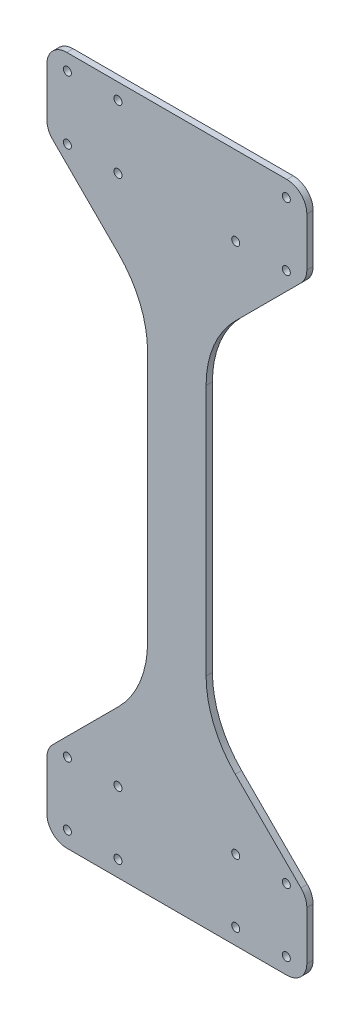
SolidWorks part; units mm, degrees
ref_plane "Front Plane" through (0, 0, 0) normal (0, 0, 1) x (1, 0, 0)
ref_plane "Top Plane" through (0, 0, 0) normal (0, 1, 0) x (1, 0, 0)
ref_plane "Right Plane" through (0, 0, 0) normal (1, 0, 0) x (0, 0, -1)
sketch "Sketch1" plane through (0, 0, 0) normal (0, 0, 1) x (1, 0, 0)
  line L0 (39.3854, -40.0501) -> (39.3854, -52.4111) construction
  line L1 (165.9345, -56.675) -> (165.9345, -42.05) construction
  line L2 (157.3152, -8.05) -> (165.9345, -16.6693)
  line L3 (157.3152, 245.3495) -> (165.9345, 253.9688)
  line L4 (39.3854, -40.0501) -> (39.3854, -52.4111)
  line L5 (165.9345, -56.675) -> (165.9345, -42.05)
  line L6 (165.9345, 245.3495) -> (39.3854, 245.3495)
  line L7 (165.9345, 279.3495) -> (165.9345, 245.3495)
  line L8 (39.3854, -52.4111) -> (165.9345, -56.675)
  line L9 (39.3854, 289.7105) -> (165.9345, 293.9745)
  line L10 (39.3854, -40.0501) -> (39.3854, -16.6693)
  line L11 (165.9345, -42.05) -> (165.9345, -16.6693)
  line L12 (157.3152, -8.05) -> (48.0047, -8.0501)
  line L13 (42.1433, 0) -> (42.1433, 237.2995) construction
  line L14 (42.1433, 118.6497) -> (215.0534, 118.6497) construction
  line L15 (165.9345, 293.9745) -> (165.9345, 279.3495)
  line L16 (39.3854, 277.3495) -> (39.3854, 245.3495)
  line L17 (39.3854, 277.3495) -> (39.3854, 289.7105)
  line L18 (102.66, -54.5431) -> (102.66, 291.8425) construction
  line L19 (102.66, 291.8425) -> (73.0854, -499321.8282) construction
  line L20 (39.3854, -16.6693) -> (89.96, 33.9052)
  line L21 (89.96, -8.05) -> (115.36, -8.05)
  line L22 (89.96, -8.05) -> (89.96, 245.3495)
  line L23 (89.96, 245.3495) -> (115.36, 245.3495)
  line L24 (115.36, -8.05) -> (115.36, 245.3495)
  line L25 (89.96, -8.05) -> (115.36, 245.3495) construction
  line L26 (89.96, 245.3495) -> (115.36, -8.05) construction
  line L27 (115.36, 33.9052) -> (157.3152, -8.05)
  line L28 (115.36, 203.3943) -> (157.3152, 245.3495)
  line L29 (39.3854, 253.9688) -> (89.96, 203.3943)
  arc A0 (157.6345, 249.9303) -> (157.6345, 253.9689) centre (157.6345, 251.9496) cw
  arc A1 (157.6345, 253.9689) -> (157.6345, 249.9303) centre (157.6345, 251.9496) cw
  arc A2 (73.0854, 249.9303) -> (73.0854, 253.9689) centre (73.0854, 251.9496) ccw
  arc A3 (73.0854, 253.9689) -> (73.0854, 249.9303) centre (73.0854, 251.9496) ccw
  arc A4 (73.0854, 249.9303) -> (73.0854, 253.9689) centre (73.0854, 251.9496) ccw
  arc A5 (73.0854, 253.9689) -> (73.0854, 249.9303) centre (73.0854, 251.9496) ccw
  arc A6 (47.6854, 249.9303) -> (47.6854, 253.9689) centre (47.6854, 251.9496) cw
  arc A7 (47.6854, 253.9689) -> (47.6854, 249.9303) centre (47.6854, 251.9496) cw
  arc A10 (47.6854, 281.6802) -> (47.6854, 285.7188) centre (47.6854, 283.6995) cw
  arc A11 (47.6854, 285.7188) -> (47.6854, 281.6802) centre (47.6854, 283.6995) cw
  arc A14 (157.6345, -48.4194) -> (157.6345, -44.3807) centre (157.6345, -46.4001) ccw
  arc A15 (157.6345, -44.3807) -> (157.6345, -48.4194) centre (157.6345, -46.4001) ccw
  arc A16 (157.6345, -48.4194) -> (157.6345, -44.3807) centre (157.6345, -46.4001) ccw
  arc A17 (157.6345, -44.3807) -> (157.6345, -48.4194) centre (157.6345, -46.4001) ccw
  arc A18 (73.0854, 281.6802) -> (73.0854, 285.7188) centre (73.0854, 283.6995) cw
  arc A19 (73.0854, 285.7188) -> (73.0854, 281.6802) centre (73.0854, 283.6995) cw
  arc A22 (157.6345, -16.6693) -> (157.6345, -12.6307) centre (157.6345, -14.65) ccw
  arc A23 (157.6345, -12.6307) -> (157.6345, -16.6693) centre (157.6345, -14.65) ccw
  arc A24 (157.6345, -16.6693) -> (157.6345, -12.6307) centre (157.6345, -14.65) ccw
  arc A25 (157.6345, -12.6307) -> (157.6345, -16.6693) centre (157.6345, -14.65) ccw
  arc A26 (73.0854, -16.6693) -> (73.0854, -12.6307) centre (73.0854, -14.65) ccw
  arc A27 (73.0854, -12.6307) -> (73.0854, -16.6693) centre (73.0854, -14.65) ccw
  arc A28 (73.0854, -16.6693) -> (73.0854, -12.6307) centre (73.0854, -14.65) ccw
  arc A29 (73.0854, -12.6307) -> (73.0854, -16.6693) centre (73.0854, -14.65) ccw
  arc A30 (73.0854, 249.9303) -> (73.0854, 253.9689) centre (73.0854, 251.9496) cw
  arc A31 (73.0854, 253.9689) -> (73.0854, 249.9303) centre (73.0854, 251.9496) cw
  arc A34 (157.6345, 249.9303) -> (157.6345, 253.9689) centre (157.6345, 251.9496) ccw
  arc A35 (157.6345, 253.9689) -> (157.6345, 249.9303) centre (157.6345, 251.9496) ccw
  arc A36 (157.6345, 249.9303) -> (157.6345, 253.9689) centre (157.6345, 251.9496) ccw
  arc A37 (157.6345, 253.9689) -> (157.6345, 249.9303) centre (157.6345, 251.9496) ccw
  arc A38 (47.6854, 249.9303) -> (47.6854, 253.9689) centre (47.6854, 251.9496) ccw
  arc A39 (47.6854, 253.9689) -> (47.6854, 249.9303) centre (47.6854, 251.9496) ccw
  arc A40 (47.6854, 249.9303) -> (47.6854, 253.9689) centre (47.6854, 251.9496) ccw
  arc A41 (47.6854, 253.9689) -> (47.6854, 249.9303) centre (47.6854, 251.9496) ccw
  arc A42 (73.0854, -48.4194) -> (73.0854, -44.3807) centre (73.0854, -46.4001) ccw
  arc A43 (73.0854, -44.3807) -> (73.0854, -48.4194) centre (73.0854, -46.4001) ccw
  arc A44 (73.0854, -48.4194) -> (73.0854, -44.3807) centre (73.0854, -46.4001) ccw
  arc A45 (73.0854, -44.3807) -> (73.0854, -48.4194) centre (73.0854, -46.4001) ccw
  arc A46 (132.2345, 249.9303) -> (132.2345, 253.9689) centre (132.2345, 251.9496) ccw
  arc A47 (132.2345, 253.9689) -> (132.2345, 249.9303) centre (132.2345, 251.9496) ccw
  arc A48 (132.2345, 249.9303) -> (132.2345, 253.9689) centre (132.2345, 251.9496) ccw
  arc A49 (132.2345, 253.9689) -> (132.2345, 249.9303) centre (132.2345, 251.9496) ccw
  arc A50 (47.6854, -48.4194) -> (47.6854, -44.3808) centre (47.6854, -46.4001) ccw
  arc A51 (47.6854, -44.3808) -> (47.6854, -48.4194) centre (47.6854, -46.4001) ccw
  arc A52 (47.6854, -48.4194) -> (47.6854, -44.3808) centre (47.6854, -46.4001) ccw
  arc A53 (47.6854, -44.3808) -> (47.6854, -48.4194) centre (47.6854, -46.4001) ccw
  arc A54 (47.6854, -16.6693) -> (47.6854, -12.6307) centre (47.6854, -14.65) ccw
  arc A55 (47.6854, -12.6307) -> (47.6854, -16.6693) centre (47.6854, -14.65) ccw
  arc A56 (47.6854, -16.6693) -> (47.6854, -12.6307) centre (47.6854, -14.65) ccw
  arc A57 (47.6854, -12.6307) -> (47.6854, -16.6693) centre (47.6854, -14.65) ccw
  arc A58 (157.6345, 281.6802) -> (157.6345, 285.7188) centre (157.6345, 283.6995) cw
  arc A59 (157.6345, 285.7188) -> (157.6345, 281.6802) centre (157.6345, 283.6995) cw
  arc A62 (132.2345, -16.6693) -> (132.2345, -12.6307) centre (132.2345, -14.65) ccw
  arc A63 (132.2345, -12.6307) -> (132.2345, -16.6693) centre (132.2345, -14.65) ccw
  arc A64 (132.2345, -16.6693) -> (132.2345, -12.6307) centre (132.2345, -14.65) ccw
  arc A65 (132.2345, -12.6307) -> (132.2345, -16.6693) centre (132.2345, -14.65) ccw
  arc A66 (132.2345, -48.4194) -> (132.2345, -44.3808) centre (132.2345, -46.4001) ccw
  arc A67 (132.2345, -44.3808) -> (132.2345, -48.4194) centre (132.2345, -46.4001) ccw
  arc A68 (132.2345, -48.4194) -> (132.2345, -44.3808) centre (132.2345, -46.4001) ccw
  arc A69 (132.2345, -44.3808) -> (132.2345, -48.4194) centre (132.2345, -46.4001) ccw
  point P62 (102.66, 118.6497)
  dimension "D3" = 0
  dimension "D2" = 25.4
  dimension "D1" = 0
  dimension "D4" = 0
  dimension "D5" = 0
  dimension "D6" = 0
  dimension "D7" = 0
  dimension "D9" = 0
  dimension "D10" = 0
  dimension "D11" = 0
  dimension "D12" = 0
  dimension "D13" = 0
  dimension "D14" = 0
extrude "Boss-Extrude1" add sketch "Sketch1" along normal blind 3.175 contours L20 L10 L4 L8 L5 L11 L2 L12 A69 A68 A65 A64 A57 A56 A53 A52 A45 A44 A29 A28 A25 A24 A17 A16 | L27 L24 L12 | L12 L24 L6 L22 | L12 L22 L20 | L16 L29 L6 L3 L7 L15 L9 L17 A49 A48 A5 A4 A0 A1 A6 A7 A10 A11 A18 A19 A58 A59 | L24 L28 L6 | L6 L29 L22
sketch "Sketch2" plane through (0, 0, 3.175) normal (0, 0, 1) x (1, 0, 0)
  line L0 (165.9345, -56.675) -> (165.9345, -16.6693) construction
  line L1 (39.3854, -52.4111) -> (84.3854, -52.4111)
  line L2 (39.3854, -52.4111) -> (39.3854, -7.4111)
  line L3 (39.3854, -7.4111) -> (84.3854, -7.4111)
  line L4 (84.3854, -52.4111) -> (84.3854, -7.4111)
  line L5 (165.9345, -52.4111) -> (120.9345, -52.4111)
  line L6 (165.9345, -52.4111) -> (165.9345, -7.4111)
  line L7 (165.9345, -7.4111) -> (120.9345, -7.4111)
  line L8 (120.9345, -52.4111) -> (120.9345, -7.4111)
  line L9 (89.96, 118.6497) -> (115.36, 118.6497) construction
  line L10 (89.96, 33.9052) -> (89.96, 203.3943) construction
  line L11 (115.36, 33.9052) -> (115.36, 203.3943) construction
  line L12 (165.9345, 289.7105) -> (120.9345, 289.7105)
  line L13 (39.3854, 289.7105) -> (84.3854, 289.7105)
  line L14 (84.3854, -52.4111) -> (120.9345, -52.4111)
  line L15 (84.3854, 289.7105) -> (120.9345, 289.7105)
  line M9 (39.3854, -52.4111) -> (165.9345, -56.675)
  line M10 (165.9345, -56.675) -> (165.9345, -16.6693)
  line M14 (165.9345, 253.9688) -> (165.9345, 293.9745)
  line M15 (165.9345, 293.9745) -> (39.3854, 289.7105)
  dimension "D1" = 45
extrude "Cut-Extrude1" cut sketch "Sketch2" against normal blind 10 contours L14 L1 L5 M9 M10 | L13 L15 L12 M14 M15
sketch "Sketch3" plane through (0, 0, 3.175) normal (0, 0, 1) x (1, 0, 0)
  line L25 (37.3854, -15.8409) -> (37.3854, -54.4111)
  line L26 (37.3854, -54.4111) -> (167.9345, -54.4111)
  line L27 (167.9345, -54.4111) -> (167.9345, -15.8409)
  line L28 (167.9345, -15.8409) -> (117.36, 34.7337)
  line L29 (117.36, 34.7337) -> (117.36, 202.5658)
  line L30 (117.36, 202.5658) -> (167.9345, 253.1404)
  line L31 (167.9345, 253.1404) -> (167.9345, 291.7105)
  line L32 (167.9345, 291.7105) -> (37.3854, 291.7105)
  line L33 (37.3854, 291.7105) -> (37.3854, 253.1404)
  line L34 (37.3854, 253.1404) -> (87.96, 202.5658)
  line L35 (87.96, 202.5658) -> (87.96, 34.7337)
  line L36 (87.96, 34.7337) -> (37.3854, -15.8409)
  line L37 (37.3854, -15.8409) -> (37.3854, -54.4111)
  line L38 (37.3854, -54.4111) -> (167.9345, -54.4111)
  line L39 (167.9345, -54.4111) -> (167.9345, -15.8409)
  line L40 (167.9345, -15.8409) -> (117.36, 34.7337)
  line L41 (117.36, 34.7337) -> (117.36, 202.5658)
  line L42 (117.36, 202.5658) -> (167.9345, 253.1404)
  line L43 (167.9345, 253.1404) -> (167.9345, 291.7105)
  line L44 (167.9345, 291.7105) -> (37.3854, 291.7105)
  line L45 (37.3854, 291.7105) -> (37.3854, 253.1404)
  line L46 (37.3854, 253.1404) -> (87.96, 202.5658)
  line L47 (87.96, 202.5658) -> (87.96, 34.7337)
  line L48 (87.96, 34.7337) -> (37.3854, -15.8409)
  circle A1 centre (132.2345, -46.4001) radius 2.0193
  circle A2 centre (132.2345, -46.4001) radius 2.0193
  circle A3 centre (132.2345, -14.65) radius 2.0193
  circle A4 centre (132.2345, -14.65) radius 2.0193
  circle A5 centre (47.6854, -14.65) radius 2.0193
  circle A6 centre (47.6854, -14.65) radius 2.0193
  circle A7 centre (47.6854, -46.4001) radius 2.0193
  circle A8 centre (47.6854, -46.4001) radius 2.0193
  circle A9 centre (73.0854, -46.4001) radius 2.0193
  circle A10 centre (73.0854, -46.4001) radius 2.0193
  circle A11 centre (73.0854, -14.65) radius 2.0193
  circle A12 centre (73.0854, -14.65) radius 2.0193
  circle A13 centre (157.6345, -14.65) radius 2.0193
  circle A14 centre (157.6345, -14.65) radius 2.0193
  circle A15 centre (157.6345, -46.4001) radius 2.0193
  circle A16 centre (157.6345, -46.4001) radius 2.0193
  circle A17 centre (132.2345, 251.9496) radius 2.0193
  circle A18 centre (132.2345, 251.9496) radius 2.0193
  circle A19 centre (73.0854, 251.9496) radius 2.0193
  circle A20 centre (73.0854, 251.9496) radius 2.0193
  circle A21 centre (157.6345, 251.9496) radius 2.0193
  circle A22 centre (157.6345, 251.9496) radius 2.0193
  circle A23 centre (47.6854, 251.9496) radius 2.0193
  circle A24 centre (47.6854, 251.9496) radius 2.0193
  circle A25 centre (47.6854, 283.6995) radius 2.0193
  circle A26 centre (47.6854, 283.6995) radius 2.0193
  circle A27 centre (73.0854, 283.6995) radius 2.0193
  circle A28 centre (73.0854, 283.6995) radius 2.0193
  circle A29 centre (157.6345, 283.6995) radius 2.0193
  circle A30 centre (157.6345, 283.6995) radius 2.0193
  dimension "D1" = 2
  dimension "D2" = 0
  dimension "D3" = 0
  dimension "D4" = 0
  dimension "D5" = 0
  dimension "D6" = 0
  dimension "D7" = 0
  dimension "D8" = 0
  dimension "D9" = 0
  dimension "D10" = 0
  dimension "D11" = 0
  dimension "D12" = 0
  dimension "D13" = 0
  dimension "D14" = 0
  dimension "D15" = 0
  dimension "D16" = 0
extrude "Boss-Extrude2" add sketch "Sketch3" against normal up to surface (3.175 mm away) up to face at (159.6538, 283.6995, 0)
fillet "Fillet1" radius 10 8 edges at (37.3854, 253.1404, 1.5875) (37.3854, 291.7105, 1.5875) (167.9345, 291.7105, 1.5875) (167.9345, 253.1404, 1.5875) (37.3854, -15.8409, 1.5875) (167.9345, -15.8409, 1.5875) (167.9345, -54.4111, 1.5875) (37.3854, -54.4111, 1.5875)
fillet "Fillet2" radius 50 4 edges at (87.96, 34.7337, 1.5875) (117.36, 34.7337, 1.5875) (87.96, 202.5658, 1.5875) (117.36, 202.5658, 1.5875)
